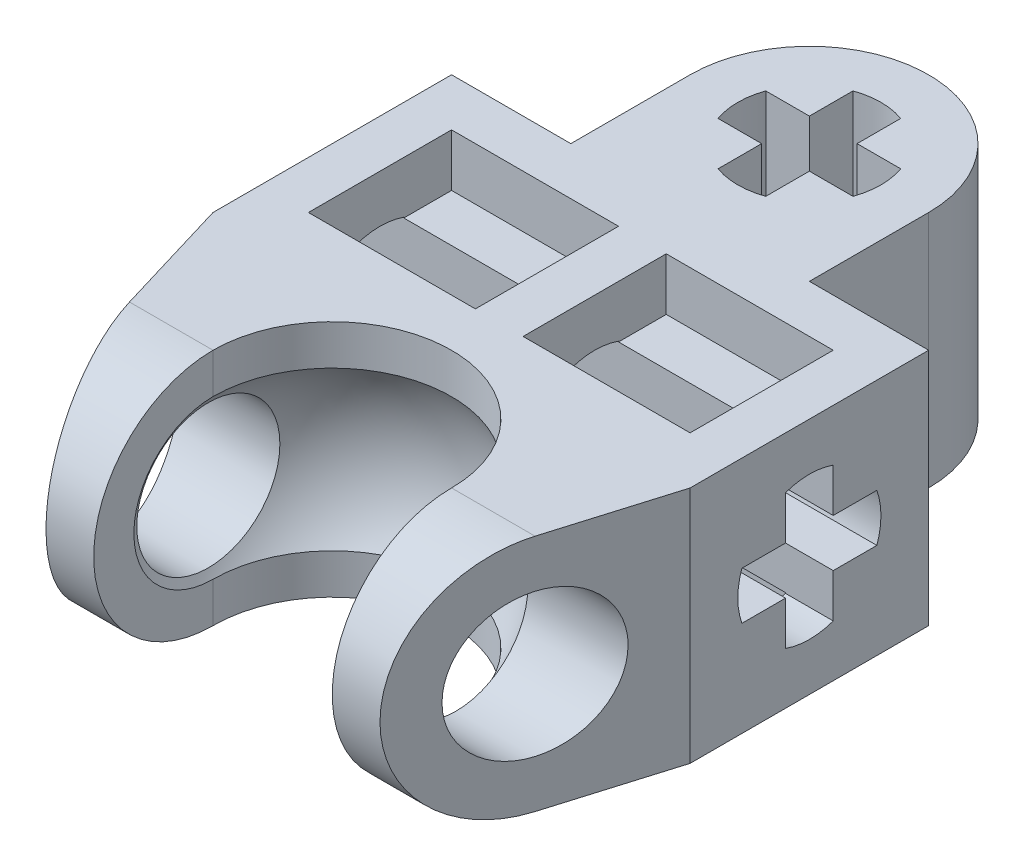
SolidWorks part; units mm, degrees
ref_plane "Front Plane" through (0, 0, 0) normal (0, 0, 1) x (1, 0, 0)
ref_plane "Top Plane" through (0, 0, 0) normal (0, 1, 0) x (1, 0, 0)
ref_plane "Right Plane" through (0, 0, 0) normal (1, 0, 0) x (0, 0, -1)
sketch "Sketch1" plane through (0, 0, 0) normal (0, 1, 0) x (1, 0, 0)
  line L1 (-5, -5) -> (5, -5)
  line L2 (-5, -5) -> (-5, 5)
  line L3 (-5, 5) -> (5, 5)
  line L4 (5, -5) -> (5, 5)
  line L5 (-5, -5) -> (5, 5) construction
  line L6 (-5, 5) -> (5, -5) construction
  line L7 (-2.5, 5) -> (2.5, 5)
  line L8 (-2.5, 5) -> (-2.5, 7.5)
  line L9 (-2.5, 7.5) -> (2.5, 7.5)
  line L10 (2.5, 5) -> (2.5, 7.5)
  line L11 (-1.5, 8) -> (1.5, 8)
  line L12 (-1.5, 8) -> (-1.5, 7)
  line L13 (-1.5, 7) -> (1.5, 7)
  line L14 (1.5, 8) -> (1.5, 7)
  line L15 (-1.5, 8) -> (1.5, 7) construction
  line L16 (-1.5, 7) -> (1.5, 8) construction
  line L17 (-0.5, 6) -> (0.5, 6)
  line L18 (-0.5, 6) -> (-0.5, 9)
  line L19 (-0.5, 9) -> (0.5, 9)
  line L20 (0.5, 6) -> (0.5, 9)
  line L21 (-0.5, 6) -> (0.5, 9) construction
  line L22 (-0.5, 9) -> (0.5, 6) construction
  circle A0 centre (0, 7.5) radius 2.5
  circle A1 centre (0, 7.5) radius 1.5
  point P0 (0, 0)
  point P6 (-2.5, 5)
  dimension "D1" = 10
  dimension "D2" = 10
  dimension "D3" = 2.5
  dimension "D4" = 5
  dimension "D5" = 2.5
  dimension "D6" = 3
  dimension "D7" = 1
extrude "Boss-Extrude1" add sketch "Sketch1" along normal blind 5 contours L1 L4 L3 L7 L2 | A0 L8 L3 | A0 L7 L10 | A1 L11 L14 L9 A0 L12 L18 L19 L20 | A1 L20 L17 L18 L13 L12 L9 A0 L14 | A1 L17 L20 | L13 A1 L18 | L20 A1 L13 | L11 A1 L20 | L18 A1 L11 | A1 L19 L18 | A1 L20 L19 | A1 L12 L13 | A1 L18 L17 | A1 L11 L12 | A1 L13 L14 | A1 L14 L11
sketch "Sketch2" plane through (0, 0, 0) normal (1, 0, 0) x (0, 0, -1)
  line L0 (-2.5, 5.5) -> (-2.5, -0.5)
  line L1 (0, 0) -> (-2.5, 0)
  line L2 (0, 0) -> (0, 5)
  line L3 (0, 5) -> (-2.5, 5)
  line L4 (-2.5, 0) -> (-2.5, 5)
  arc A0 (-2.5, -0.5) -> (-2.5, 5.5) centre (-2.5, 2.5) ccw
  dimension "D3" = 6
  dimension "D1" = 2.5
  dimension "D2" = 5
revolve "Cut-Revolve3" cut sketch "Sketch2" angle 360 about L0
sketch "Sketch3" plane through (5, 0, 0) normal (1, 0, 0) x (0, 0, -1)
  line L0 (-5, 5) -> (5, 5) construction
  line L1 (-5, 5) -> (-5, 0) construction
  circle A0 centre (-2.5, 2.5) radius 1.5
  dimension "D1" = 2.5
  dimension "D3" = 3
  dimension "D2" = 2.5
extrude "Cut-Extrude1" cut sketch "Sketch3" against normal blind 10
sketch "Sketch4" plane through (0, 5, 0) normal (0, 1, 0) x (1, 0, 0)
  line L0 (-5, 0) -> (-3.5, -5)
  line L1 (-5, -5) -> (-5, 5) construction
  line L2 (-5, -5) -> (5, -5) construction
  line L3 (5, 0) -> (3.5, -5)
  line L4 (5, -5) -> (5, 5) construction
  line L5 (5, 0) -> (5, -5)
  line L6 (5, -5) -> (3.5, -5)
  line L7 (-3.5, -5) -> (-5, -5)
  line L8 (-5, -5) -> (-5, 0)
  dimension "D1" = 1.5
  dimension "D2" = 1.5
extrude "Cut-Extrude2" cut sketch "Sketch4" against normal up to next
sketch "Sketch5" plane through (0, 5, 0) normal (0, 1, 0) x (1, 0, 0)
  line L0 (-3.5, -5) -> (3.5, -5) construction
  line L1 (-2.5, -2.5) -> (2.5, -2.5)
  line L2 (-2.5, -2.5) -> (-2.5, -5)
  line L3 (-2.5, -5) -> (2.5, -5)
  line L4 (2.5, -2.5) -> (2.5, -5)
  line L5 (-2.5, -2.5) -> (2.5, -5) construction
  line L6 (-2.5, -5) -> (2.5, -2.5) construction
  circle A0 centre (0, -2.5) radius 2.5
  point P0 (0, -3.75)
  point P7 (0, -5)
  line M13 (-3.5, -5) -> (3.5, -5)
  circle M14 centre (0, -2.5) radius 1.6583
  dimension "D1" = 5
  dimension "D2" = 2.5
extrude "Cut-Extrude4" cut sketch "Sketch5" against normal blind 10 contours A0 L1 M14 | L1 A0 M14 | A0 L3 L4 | A0 L2 M13
sketch "Sketch6" plane through (-2.5, 0, 0) normal (1, 0, 0) x (0, 0, -1)
  line L0 (-2.5, 5) -> (-5, 5) construction
  line L1 (-5, 0) -> (-5, 5) construction
  line L3 (-2.5, 5) -> (-5, 5)
  line L4 (-2.5, 5) -> (-2.5, 0)
  line L5 (-2.5, 0) -> (-5, 0)
  line L6 (-5, 5) -> (-5, 0)
  circle A0 centre (-2.5, 2.5) radius 2.5
  line M4 (-2.5, 5) -> (-5, 5)
  line M5 (-5, 5) -> (-5, 0)
  line M6 (-5, 0) -> (-2.5, 0)
  dimension "D3" = 5
  dimension "D1" = 2.5
  dimension "D2" = 2.5
extrude "Cut-Extrude5" cut sketch "Sketch6" against normal blind 10 and the other way blind 10 contours A0 M4 M5 | A0 L6 M6
sketch "Sketch7" plane through (-5, 0, 0) normal (-1, 0, 0) x (0, 0, 1)
  line L0 (-5, 0) -> (0, 5)
  line L1 (-2, 1) -> (-3, 1)
  line L2 (-2, 1) -> (-2, 4)
  line L3 (-2, 4) -> (-3, 4)
  line L4 (-3, 1) -> (-3, 4)
  line L5 (-2, 1) -> (-3, 4) construction
  line L6 (-2, 4) -> (-3, 1) construction
  line L8 (-1, 2) -> (-4, 2)
  line L9 (-1, 2) -> (-1, 3)
  line L10 (-1, 3) -> (-4, 3)
  line L11 (-4, 2) -> (-4, 3)
  line L12 (-1, 2) -> (-4, 3) construction
  line L13 (-1, 3) -> (-4, 2) construction
  circle A0 centre (-2.5, 2.5) radius 1.5
  point P0 (-2.5, 2.5)
  point P10 (-2.5, 2.5)
  point P11 (-2.5, 2.5)
  dimension "D1" = 1
  dimension "D2" = 3
extrude "Cut-Extrude6" cut sketch "Sketch7" against normal blind 10 contours L10 A0 L8 L4 | L0 L10 L4 | L2 A0 L4 L10 | L8 L2 L0 | A0 L10 L2 L8 | L4 A0 L2 L8
sketch "Sketch8" plane through (0, 5, 0) normal (0, 1, 0) x (1, 0, 0)
  line L0 (-5, 5) -> (-2.5, 5) construction
  line L1 (-4, 4) -> (4, 4)
  line L2 (-4, 4) -> (-4, 1)
  line L3 (-4, 1) -> (4, 1)
  line L4 (4, 4) -> (4, 1)
  line L5 (-5, 0) -> (-5, 5) construction
  line L6 (5, 0) -> (5, 5) construction
  line L8 (-0.5, 4) -> (0.5, 4)
  line L9 (-0.5, 4) -> (-0.5, 1)
  line L10 (-0.5, 1) -> (0.5, 1)
  line L11 (0.5, 4) -> (0.5, 1)
  dimension "D1" = 1
  dimension "D2" = 1
  dimension "D3" = 1
  dimension "D4" = 3
  dimension "D5" = 1
  dimension "D6" = 3.5
extrude "Cut-Extrude13" cut sketch "Sketch8" against normal blind 1.1 contours L1 L11 L3 L4 | L9 L1 L2 L3
sketch "Sketch9" plane through (0, 0, 0) normal (0, -1, 0) x (-1, 0, 0)
  line L0 (-2.5, 5) -> (-5, 5) construction
  line L1 (-4, 1) -> (4, 1)
  line L2 (-4, 1) -> (-4, 4)
  line L3 (-4, 4) -> (4, 4)
  line L4 (4, 1) -> (4, 4)
  line L5 (-4, 1) -> (4, 4) construction
  line L6 (-4, 4) -> (4, 1) construction
  line L7 (-5, 0) -> (-5, 5) construction
  line L8 (5, 0) -> (5, 5) construction
  line L10 (-0.5, 1) -> (0.5, 1)
  line L11 (-0.5, 1) -> (-0.5, 4)
  line L12 (-0.5, 4) -> (0.5, 4)
  line L13 (0.5, 1) -> (0.5, 4)
  line L14 (-0.5, 1) -> (0.5, 4) construction
  line L15 (-0.5, 4) -> (0.5, 1) construction
  point P0 (0, 2.5)
  point P11 (0, 2.5)
  dimension "D1" = 1
  dimension "D2" = 1
  dimension "D3" = 1
  dimension "D4" = 3
  dimension "D5" = 1
extrude "Cut-Extrude14" cut sketch "Sketch9" against normal blind 1.1 contours L1 L11 L3 L2 | L13 L1 L4 L3
equation "\"u\"= 1"
equation "\"sphere\"= 6"
equation "\"D3@Sketch2\"=\"sphere\""
